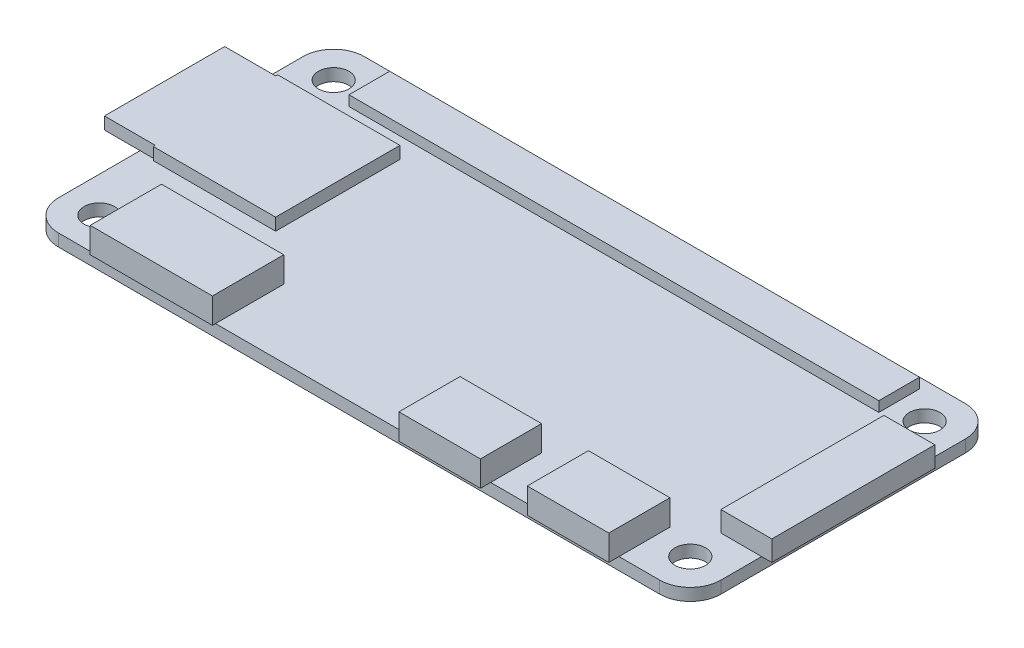
SolidWorks part; units mm, degrees
ref_plane "Front" through (0, 0, 0) normal (0, 0, 1) x (1, 0, 0)
ref_plane "Top" through (0, 0, 0) normal (0, 1, 0) x (1, 0, 0)
ref_plane "Right" through (0, 0, 0) normal (1, 0, 0) x (0, 0, -1)
sketch "Sketch1" plane through (0, 0, 0) normal (0, 1, 0) x (1, 0, 0)
  line L1 (0, 0) -> (65, 0)
  line L2 (0, 0) -> (0, -30)
  line L3 (0, -30) -> (65, -30)
  line L4 (65, 0) -> (65, -30)
  dimension "D1" = 65
  dimension "D2" = 30
extrude "Boss-Extrude1" add sketch "Sketch1" along normal blind 1.2
sketch "Sketch2" plane through (0, 1.2, 0) normal (0, 1, 0) x (1, 0, 0)
  line L0 (0, -30) -> (65, -30) construction
  line L1 (0, 0) -> (0, -30) construction
  circle A0 centre (3.5, -26.5) radius 1.5
  circle A1 centre (61.5, -26.5) radius 1.5
  circle A2 centre (61.5, -3.5) radius 1.5
  circle A3 centre (3.5, -3.5) radius 1.5
  dimension "D3" = 3
  dimension "D4" = 2
  dimension "D1" = 3.5
  dimension "D2" = 3.5
  dimension "D5" = 2
extrude "Cut-Extrude1" cut sketch "Sketch2" against normal through all
fillet "Fillet1" radius 3 4 edges at (65, 0.6, 30) (65, 0.6, 0) (0, 0.6, 0) (0, 0.6, 30)
sketch "Sketch3" plane through (0, 1.2, 0) normal (0, 1, 0) x (1, 0, 0)
  line L0 (3, -30) -> (62, -30) construction
  line L1 (1.5, -7) -> (13.5, -7)
  line L2 (1.5, -7) -> (1.5, -19.2)
  line L3 (1.5, -19.2) -> (13.5, -19.2)
  line L4 (13.5, -7) -> (13.5, -19.2)
  line L5 (62, 0) -> (3, 0) construction
  line L6 (0, -3) -> (0, -27) construction
  point P4 (1.5, -13.1)
  dimension "D1" = 16.9
  dimension "D2" = 7
  dimension "D3" = 1.5
  dimension "D4" = 12
extrude "Boss-Extrude2" add sketch "Sketch3" along normal blind 1.2
sketch "Sketch4" plane through (1.5, 0, 0) normal (-1, 0, 0) x (0, 0, 1)
  line L0 (7, 1.2) -> (19.2, 1.2) construction
  line L1 (7.2, 1.2) -> (19, 1.2)
  line L2 (7.2, 1.2) -> (7.2, 2.4)
  line L3 (7.2, 2.4) -> (19, 2.4)
  line L4 (19, 1.2) -> (19, 2.4)
  line L5 (7, 2.4) -> (19.2, 2.4) construction
  line L7 (7, 2.4) -> (7, 1.2) construction
  line L8 (19.2, 2.4) -> (19.2, 1.2) construction
  dimension "D1" = 0.2
  dimension "D2" = 0.2
extrude "Boss-Extrude3" add sketch "Sketch4" along normal blind 5
sketch "Sketch5" plane through (0, 1.2, 0) normal (0, 1, 0) x (1, 0, 0)
  line L0 (0, -19) -> (0, -27) construction
  line L1 (6.4, -23.3) -> (18.4, -23.3)
  line L2 (6.4, -23.3) -> (6.4, -30.3)
  line L3 (6.4, -30.3) -> (18.4, -30.3)
  line L4 (18.4, -23.3) -> (18.4, -30.3)
  line L5 (3, -30) -> (62, -30) construction
  point P4 (12.4, -23.3)
  dimension "D1" = 12.4
  dimension "D2" = 12
  dimension "D3" = 7
  dimension "D4" = 0.3
extrude "Boss-Extrude4" add sketch "Sketch5" along normal blind 2.5
sketch "Sketch6" plane through (0, 1.2, 0) normal (0, 1, 0) x (1, 0, 0)
  line L0 (0, -19) -> (0, -27) construction
  line L1 (37.4, -25) -> (45.4, -25)
  line L2 (37.4, -25) -> (37.4, -31)
  line L3 (37.4, -31) -> (45.4, -31)
  line L4 (45.4, -25) -> (45.4, -31)
  line L5 (50, -25) -> (58, -25)
  line L6 (50, -25) -> (50, -31)
  line L7 (50, -31) -> (58, -31)
  line L8 (58, -25) -> (58, -31)
  line L9 (18.4, -30) -> (62, -30) construction
  point P8 (41.4, -25)
  point P11 (54, -25)
  dimension "D1" = 41.4
  dimension "D2" = 54
  dimension "D3" = 8
  dimension "D4" = 8
  dimension "D5" = 6
  dimension "D6" = 1
  dimension "D7" = 1
  dimension "D8" = 6
extrude "Boss-Extrude5" add sketch "Sketch6" along normal blind 2.5
sketch "Sketch7" plane through (0, 1.2, 0) normal (0, 1, 0) x (1, 0, 0)
  line L0 (58, -30) -> (62, -30) construction
  line L1 (66, -7) -> (61, -7)
  line L2 (66, -7) -> (66, -23)
  line L3 (66, -23) -> (61, -23)
  line L4 (61, -7) -> (61, -23)
  line L5 (65, -27) -> (65, -3) construction
  point P4 (61, -15)
  dimension "D1" = 15
  dimension "D2" = 1
  dimension "D3" = 16
  dimension "D4" = 5
extrude "Boss-Extrude6" add sketch "Sketch7" along normal blind 2
sketch "Sketch8" plane through (0, 1.2, 0) normal (0, 1, 0) x (1, 0, 0)
  line L1 (6.5, -1) -> (58.5, -1)
  line L2 (6.5, -1) -> (6.5, -5)
  line L3 (6.5, -5) -> (58.5, -5)
  line L4 (58.5, -1) -> (58.5, -5)
  line L5 (62, 0) -> (3, 0) construction
  circle A0 centre (3.5, -3.5) radius 1.5 construction
  point P4 (32.5, -1)
  dimension "D1" = 29
  dimension "D2" = 1
  dimension "D3" = 52
  dimension "D4" = 4
extrude "Boss-Extrude7" add sketch "Sketch8" along normal blind 1
